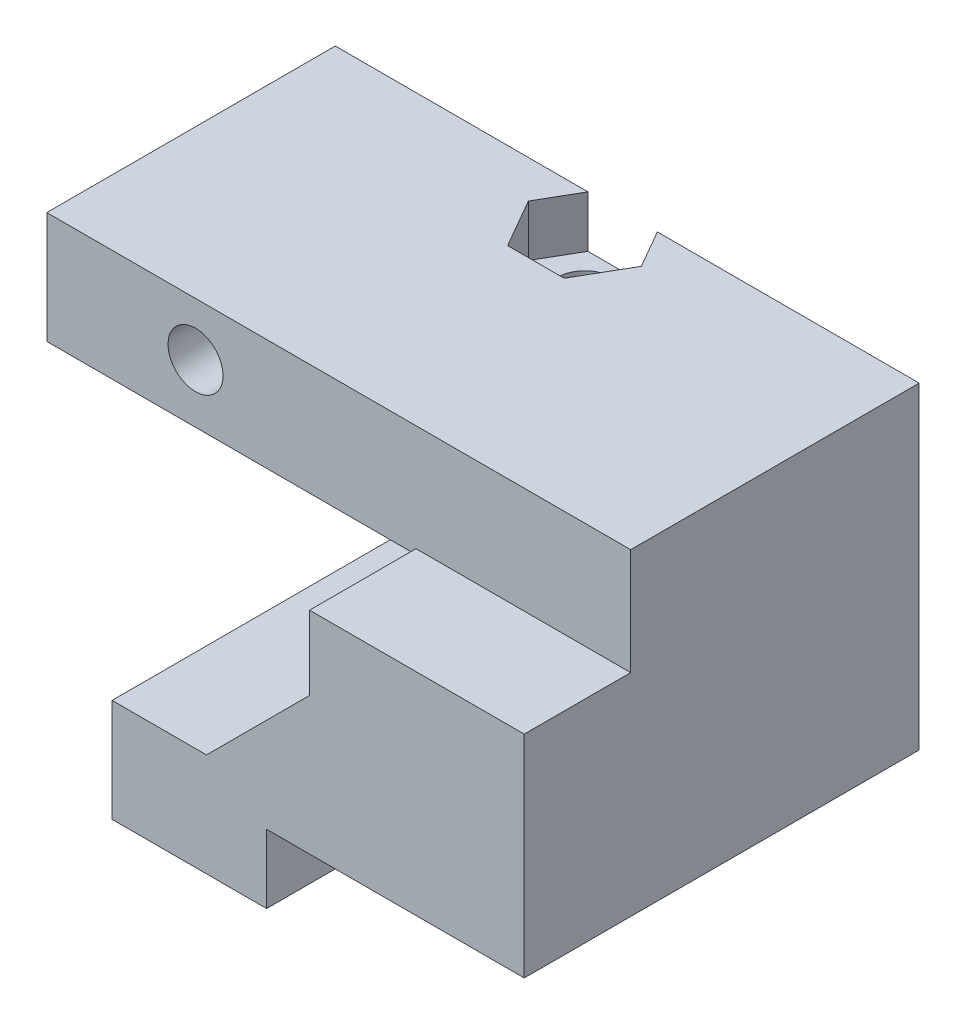
SolidWorks part; units mm, degrees
ref_plane "Alzado" through (0, 0, 0) normal (0, 0, 1) x (1, 0, 0)
ref_plane "Planta" through (0, 0, 0) normal (0, 1, 0) x (1, 0, 0)
ref_plane "Vista lateral" through (0, 0, 0) normal (1, 0, 0) x (0, 0, -1)
sketch "Croquis1" plane through (0, 0, 0) normal (0, 0, 1) x (1, 0, 0)
  line L0 (0, 0) -> (9, 0)
  line L1 (9, 0) -> (9, 4)
  line L2 (9, 4) -> (24, 4)
  line L3 (24, 4) -> (24, 22.5)
  line L4 (24, 22.5) -> (-10, 22.5)
  line L5 (-10, 22.5) -> (-10, 16)
  line L6 (-10, 16) -> (11.5, 16)
  line L7 (11.5, 16) -> (11.5, 6)
  line L8 (11.5, 6) -> (0, 6)
  line L9 (0, 6) -> (0, 0)
  dimension "D1" = 24
  dimension "D2" = 4
  dimension "D3" = 9
  dimension "D4" = 22.5
  dimension "D5" = 21.5
  dimension "D6" = 6.5
  dimension "D7" = 6
  dimension "D8" = 10
extrude "Saliente-Extruir1" add sketch "Croquis1" along normal blind 23
sketch "Croquis2" plane through (0, 0, 23) normal (0, 0, 1) x (1, 0, 0)
  line L0 (24, 4) -> (24, 22.5) construction
  line L1 (-10, 22.5) -> (24, 22.5)
  line L2 (-10, 22.5) -> (-10, 16.3)
  line L3 (-10, 16.3) -> (24, 16.3)
  line L4 (24, 22.5) -> (24, 16.3)
  dimension "D1" = 6.2
extrude "Cortar-Extruir1" cut sketch "Croquis2" against normal blind 6.2
sketch "Croquis3" plane through (0, 0, 23) normal (0, 0, 1) x (1, 0, 0)
  line L1 (11.5, 16) -> (-10, 16)
  line L2 (11.5, 16) -> (11.5, 16.3)
  line L3 (11.5, 16.3) -> (-10, 16.3)
  line L4 (-10, 16) -> (-10, 16.3)
extrude "Cortar-Extruir2" cut sketch "Croquis3" against normal up to surface (6.2 mm away) up to face at (7, 19.4, 16.8)
sketch "Croquis4" plane through (0, 0, 16.8) normal (0, 0, 1) x (1, 0, 0)
  line L0 (-10, 19.4) -> (-1.34, 19.4) construction
  line L2 (24, 22.5) -> (-10, 22.5) construction
  line L3 (-10, 22.5) -> (-10, 16) construction
  circle A0 centre (-1.34, 19.4) radius 1.6
  dimension "D1" = 3.2
  dimension "D2" = 8.66
  dimension "D3" = 3.1
extrude "Cortar-Extruir3" cut sketch "Croquis4" against normal up to next
sketch "Croquis5" plane through (0, 0, 0) normal (0, 0, -1) x (-1, 0, 0)
  line L1 (-1.9509, 19.4) -> (-0.3054, 16.55)
  line L2 (-0.3054, 16.55) -> (2.9854, 16.55)
  line L3 (2.9854, 16.55) -> (4.6309, 19.4)
  line L4 (4.6309, 19.4) -> (2.9854, 22.25)
  line L5 (2.9854, 22.25) -> (-0.3054, 22.25)
  line L6 (-0.3054, 22.25) -> (-1.9509, 19.4)
  circle A0 centre (1.34, 19.4) radius 2.85 construction
  dimension "D1" = 5.7
extrude "Cortar-Extruir4" cut sketch "Croquis5" against normal offset from surface (9.8 mm away) 7 up to face at (0.26, 19.4, 16.8)
sketch "Croquis6" plane through (0, 16, 0) normal (0, -1, 0) x (1, 0, 0)
  line L0 (0.26, 16.8) -> (-2.94, 16.8) construction
  line L1 (0.26, 16.8) -> (-2.94, 16.8) construction
  line L2 (-1.34, 16.8) -> (-1.34, 2.2) construction
  line L3 (-1.34, 2.2) -> (6.73, 2.2) construction
  circle A0 centre (6.73, 2.2) radius 1.6
  dimension "D1" = 3.2
  dimension "D2" = 8.07
  dimension "D3" = 14.6
extrude "Cortar-Extruir5" cut sketch "Croquis6" against normal up to next
sketch "Croquis7" plane through (0, 0, 0) normal (0, -1, 0) x (1, 0, 0)
  line L0 (0, 0) -> (9, 0) construction
  line L1 (0, 23) -> (0, 0) construction
  circle A0 centre (4.95, 3.3) radius 1.6
  dimension "D1" = 3.2
  dimension "D2" = 3.3
  dimension "D3" = 4.95
extrude "Cortar-Extruir6" cut sketch "Croquis7" against normal up to next
sketch "Croquis10" plane through (0, 0, 0) normal (0, 0, -1) x (-1, 0, 0)
  line L0 (-11.5, 6) -> (-5.5, 6)
  line L1 (-11.5, 6) -> (0, 6) construction
  line L2 (-5.5, 6) -> (-11.5, 12)
  line L3 (-11.5, 16) -> (-11.5, 6) construction
  line L4 (-11.5, 12) -> (-11.5, 6)
  dimension "D1" = 45
  dimension "D2" = 6
extrude "Saliente-Extruir2" add sketch "Croquis10" against normal up to surface (23 mm away) up to face at (11.125, 6.575, 23)
sketch "Croquis8" plane through (0, 6, 0) normal (0, 1, 0) x (1, 0, 0)
  line L1 (1.6591, -3.3) -> (3.3046, -6.15)
  line L2 (3.3046, -6.15) -> (6.5954, -6.15)
  line L3 (6.5954, -6.15) -> (8.2409, -3.3)
  line L4 (8.2409, -3.3) -> (6.5954, -0.45)
  line L5 (6.5954, -0.45) -> (3.3046, -0.45)
  line L6 (3.3046, -0.45) -> (1.6591, -3.3)
  circle A0 centre (4.95, -3.3) radius 2.85 construction
  dimension "D1" = 5.7
extrude "Cortar-Extruir7" cut sketch "Croquis8" against normal blind 4 and the other way up to next
sketch "Croquis9" plane through (0, 22.5, 0) normal (0, 1, 0) x (1, 0, 0)
  line L1 (3.4391, -2.2) -> (5.0846, -5.05)
  line L2 (5.0846, -5.05) -> (8.3754, -5.05)
  line L3 (8.3754, -5.05) -> (10.0209, -2.2)
  line L4 (10.0209, -2.2) -> (8.3754, 0.65)
  line L5 (8.3754, 0.65) -> (5.0846, 0.65)
  line L6 (5.0846, 0.65) -> (3.4391, -2.2)
  circle A0 centre (6.73, -2.2) radius 2.85 construction
  dimension "D1" = 5.7
extrude "Cortar-Extruir8" cut sketch "Croquis9" against normal blind 3
